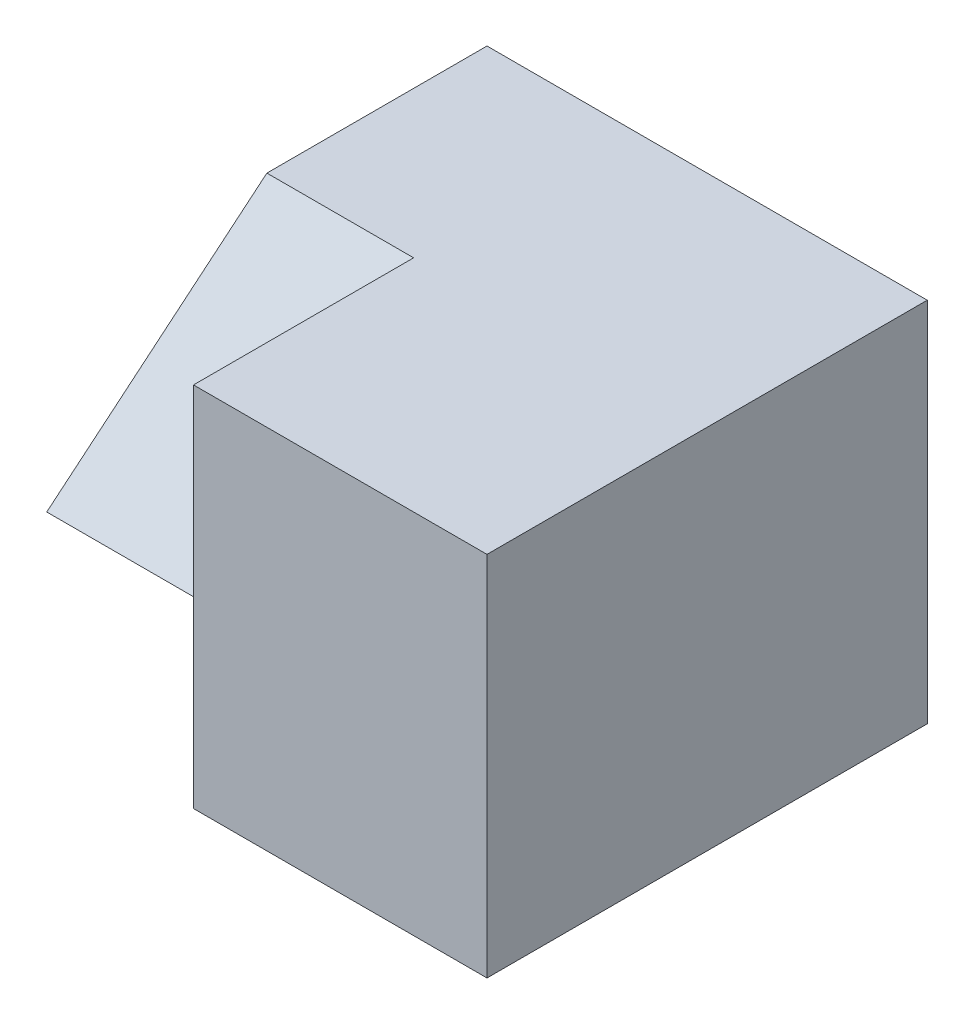
SolidWorks part; units mm, degrees
ref_plane "Front" through (0, 0, 0) normal (0, 0, 1) x (1, 0, 0)
ref_plane "Top" through (0, 0, 0) normal (0, 1, 0) x (1, 0, 0)
ref_plane "Right" through (0, 0, 0) normal (1, 0, 0) x (0, 0, -1)
sketch "Sketch1" plane through (0, 0, 0) normal (0, 1, 0) x (1, 0, 0)
  line L1 (-3, -3) -> (3, -3)
  line L2 (-3, -3) -> (-3, 3)
  line L3 (-3, 3) -> (3, 3)
  line L4 (3, -3) -> (3, 3)
  line L5 (-3, -3) -> (3, 3) construction
  line L6 (-3, 3) -> (3, -3) construction
  point P0 (0, 0)
  dimension "D1" = 6
  dimension "D2" = 6
extrude "Boss-Extrude1" add sketch "Sketch1" along normal blind 5
sketch "Sketch2" plane through (-3, 0, 0) normal (-1, 0, 0) x (0, 0, 1)
  line L0 (0, 5) -> (3, 2.5)
  line L3 (3, 2.5) -> (0, 0)
  line L7 (-3, 0) -> (3, 0)
  line L8 (3, 0) -> (3, 5)
  line L9 (3, 5) -> (-3, 5)
  line L10 (-3, 5) -> (-3, 0)
  line L11 (-3, 0) -> (3, 0)
  line L12 (3, 0) -> (3, 5)
  line L13 (3, 5) -> (-3, 5)
  line L14 (-3, 5) -> (-3, 0)
  dimension "D1" = 0
extrude "Cut-Extrude1" cut sketch "Sketch2" against normal blind 2
